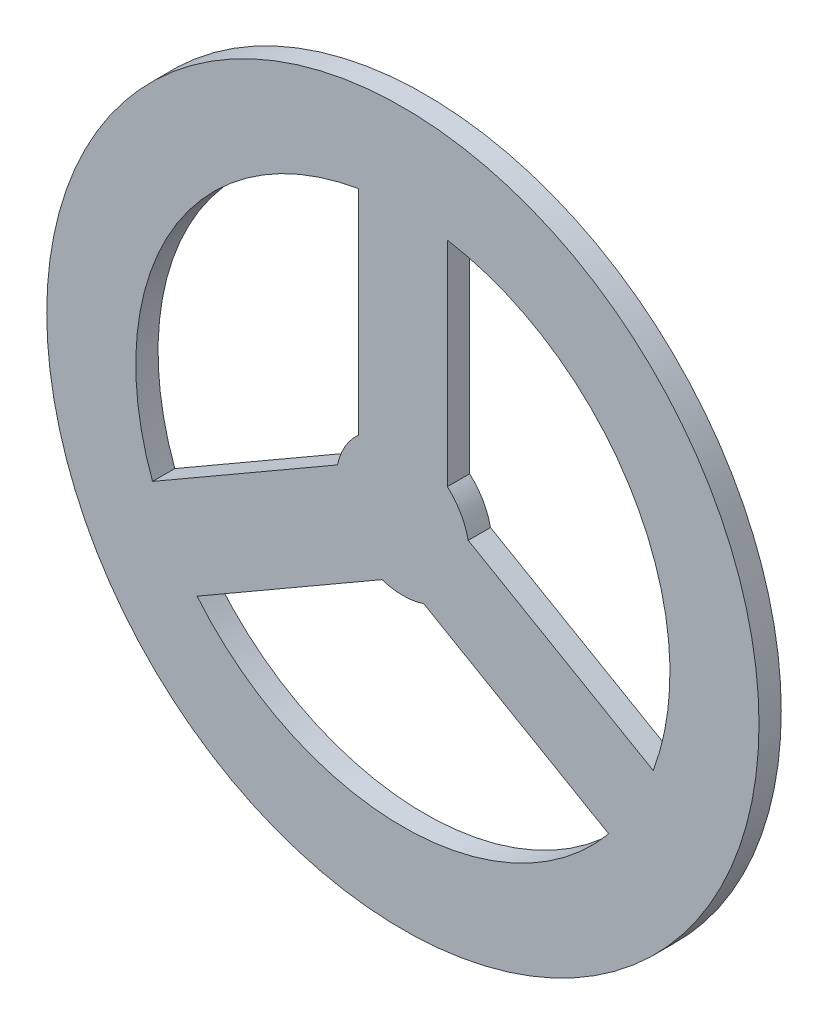
SolidWorks part; units mm, degrees
ref_plane "Front Plane" through (0, 0, 0) normal (0, 0, 1) x (1, 0, 0)
ref_plane "Top Plane" through (0, 0, 0) normal (0, 1, 0) x (1, 0, 0)
ref_plane "Right Plane" through (0, 0, 0) normal (1, 0, 0) x (0, 0, -1)
sketch "Sketch1" plane through (0, 0, 0) normal (0, 0, 1) x (1, 0, 0)
  line L1 (-12.7, 14.199) -> (-12.7, 75.1342)
  line L2 (12.7, 14.199) -> (12.7, 75.1342)
  line L4 (18.6467, 3.899) -> (71.4181, -26.5686)
  line L5 (5.9467, -18.098) -> (58.7181, -48.5656)
  line L6 (-5.9467, -18.098) -> (-58.7181, -48.5656)
  line L7 (-18.6467, 3.899) -> (-71.4181, -26.5686)
  arc A0 (-12.7, 14.199) -> (-18.6467, 3.899) centre (0, 0) ccw
  circle A1 centre (0, 0) radius 101.6
  arc A2 (-12.7, 75.1342) -> (-71.4181, -26.5686) centre (0, 0) ccw
  arc A3 (-58.7181, -48.5656) -> (58.7181, -48.5656) centre (0, 0) ccw
  arc A4 (-5.9467, -18.098) -> (5.9467, -18.098) centre (0, 0) ccw
  arc A5 (18.6467, 3.899) -> (12.7, 14.199) centre (0, 0) ccw
  arc A6 (71.4181, -26.5686) -> (12.7, 75.1342) centre (0, 0) ccw
  point P21 (0, 0)
  dimension "D1" = 38.1
  dimension "D2" = 203.2
  dimension "D3" = 152.4
  dimension "D4" = 3
extrude "Boss-Extrude1" add sketch "Sketch1" along normal blind 6.35
scale "Scale1" scale about centroid uniform scaling yes scale factor 0.4
